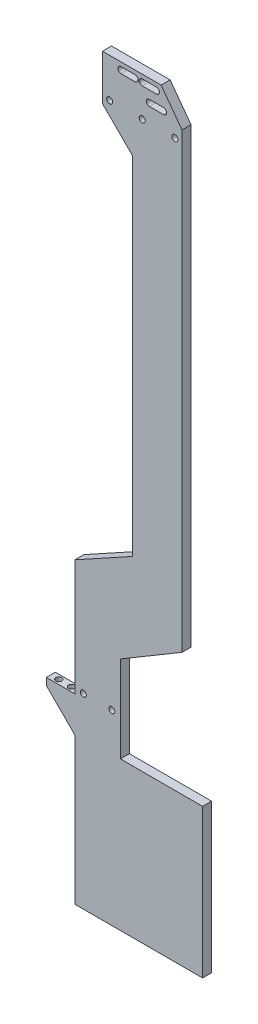
SolidWorks part; units mm, degrees
material "1060 Alloy"
ref_plane "Front Plane" through (0, 0, 0) normal (0, 0, 1) x (1, 0, 0)
ref_plane "Top Plane" through (0, 0, 0) normal (0, 1, 0) x (1, 0, 0)
ref_plane "Right Plane" through (0, 0, 0) normal (1, 0, 0) x (0, 0, -1)
sketch "Sketch1" plane through (0, 0, 0) normal (0, 0, 1) x (1, 0, 0)
  line L0 (-14.5, 164.7863) -> (-29.2, 184.7863) construction
  line L1 (-70.5, 184.7863) -> (-29.2, 184.7863) construction
  line L2 (-70.5, 184.7863) -> (-70.5, 152.7863) construction
  line L3 (-14.5, 164.7863) -> (-14.5, -153.7918) construction
  line L4 (-70.5, 152.7863) -> (-49.5, 131.7863) construction
  line L5 (-49.5, 131.7863) -> (-49.5, -112.8034) construction
  line L6 (-90, -135.1126) -> (-49.5, -112.8034) construction
  line L7 (-14.5, -153.7918) -> (-57.9145, -179.5263) construction
  line L9 (0, -345.1126) -> (-90, -345.1126) construction
  line L11 (-14.5, 164.7863) -> (-29.2, 184.7863)
  line L12 (-70.5, 184.7863) -> (-29.2, 184.7863)
  line L13 (-70.5, 184.7863) -> (-70.5, 152.7863)
  line L14 (-14.5, 164.7863) -> (-14.5, -153.7918)
  line L15 (-70.5, 152.7863) -> (-49.5, 131.7863)
  line L16 (-49.5, 131.7863) -> (-49.5, -112.8034)
  line L17 (-90, -135.1126) -> (-49.5, -112.8034)
  line L18 (-14.5, -153.7918) -> (-57.9145, -179.5263)
  line L19 (-57.9145, -179.5263) -> (-57.9145, -240.4418)
  line L20 (0, -345.1126) -> (-90, -345.1126)
  line L21 (-90, -345.1126) -> (-90, -241.825)
  line L22 (-42.5, 179.7863) -> (-32.5, 179.7863) construction
  line L23 (-42.5, 181.9363) -> (-32.5, 181.9363)
  line L24 (-42.5, 177.6363) -> (-32.5, 177.6363)
  line L25 (-57.5, 179.7863) -> (-47.5, 179.7863) construction
  line L26 (-32.5, 179.7863) -> (-32.5, 175.88) construction
  line L27 (-57.5, 181.9363) -> (-47.5, 181.9363)
  line L28 (-57.5, 177.6363) -> (-47.5, 177.6363)
  line L29 (-37.5, 169.7863) -> (-27.5, 169.7863) construction
  line L30 (-37.5, 171.9363) -> (-27.5, 171.9363)
  line L31 (-37.5, 167.6363) -> (-27.5, 167.6363)
  line L32 (-32.5, 169.7863) -> (-52.5, 169.7863) construction
  line L33 (-32.5, 175.88) -> (-37.5, 175.88) construction
  line L34 (-37.5, 179.7863) -> (-37.5, 175.88) construction
  line L35 (-47.5, 179.7863) -> (-47.5, 175.4879) construction
  line L36 (-47.5, 175.4879) -> (-52.5, 175.4879) construction
  line L37 (-32.5, 174.0404) -> (-32.5, 169.7863) construction
  line L38 (-27.5, 169.7863) -> (-27.5, 174.0404) construction
  line L39 (-27.5, 174.0404) -> (-32.5, 174.0404) construction
  line L40 (-52.5, 175.4879) -> (-52.5, 179.7863) construction
  line L41 (-57.9145, -240.4418) -> (0, -240.4418)
  line L42 (0, -240.4418) -> (0, -345.1126)
  line L43 (-57.9145, -240.4418) -> (0, -240.4418) construction
  line L44 (-90, -216.825) -> (-110, -216.825) construction
  line L45 (-110, -216.825) -> (-110, -221.825) construction
  line L46 (-110, -221.825) -> (-90, -241.825) construction
  line L47 (-90, -216.825) -> (-110, -216.825)
  line L48 (-110, -216.825) -> (-110, -221.825)
  line L49 (-110, -221.825) -> (-90, -241.825)
  line L50 (-90, -216.825) -> (-90, -135.1126)
  line L51 (-90, -216.825) -> (-57.9145, -216.825) construction
  line L52 (-90, -213.65) -> (-57.9145, -213.65) construction
  circle A0 centre (-19.5, 157.2863) radius 2.15 construction
  circle A1 centre (-42.5, 157.2863) radius 2.15 construction
  circle A2 centre (-65.5, 157.2863) radius 2.15 construction
  circle A3 centre (-37.5, 179.7863) radius 2.15 construction
  circle A4 centre (-52.5, 179.7863) radius 2.15 construction
  circle A5 centre (-32.5, 169.7863) radius 2.15 construction
  circle A6 centre (-19.5, 157.2863) radius 2.15
  circle A7 centre (-42.5, 157.2863) radius 2.15
  circle A8 centre (-65.5, 157.2863) radius 2.15
  circle A9 centre (-37.5, 179.7863) radius 2.15 construction
  circle A10 centre (-52.5, 179.7863) radius 2.15 construction
  circle A11 centre (-32.5, 169.7863) radius 2.15 construction
  arc A12 (-42.5, 181.9363) -> (-42.5, 177.6363) centre (-42.5, 179.7863) ccw
  arc A13 (-32.5, 177.6363) -> (-32.5, 181.9363) centre (-32.5, 179.7863) ccw
  arc A14 (-57.5, 181.9363) -> (-57.5, 177.6363) centre (-57.5, 179.7863) ccw
  arc A15 (-47.5, 177.6363) -> (-47.5, 181.9363) centre (-47.5, 179.7863) ccw
  arc A16 (-37.5, 171.9363) -> (-37.5, 167.6363) centre (-37.5, 169.7863) ccw
  arc A17 (-27.5, 167.6363) -> (-27.5, 171.9363) centre (-27.5, 169.7863) ccw
  circle A18 centre (-84, -213.65) radius 2.1
  circle A19 centre (-63.9145, -213.65) radius 2.1
  point P31 (-37.5, 179.7863)
  point P36 (-52.5, 179.7863)
  point P45 (-32.5, 169.7863)
  dimension "D4" = 4.2
  dimension "D1" = 5
  dimension "D2" = 5
  dimension "D3" = 3.175
  dimension "D5" = 6
  dimension "D6" = 6
extrude "Boss-Extrude1" add sketch "Sketch1" along normal blind 6.35
sketch "Sketch2" plane through (0, -216.825, 0) normal (0, 1, 0) x (-1, 0, 0)
  line L0 (90, 3.175) -> (95.5, 3.175) construction
  line L1 (90, 6.35) -> (90, 0) construction
  line L2 (95.5, 3.175) -> (104.5, 3.175) construction
  line L3 (104.5, 3.175) -> (110, 3.175) construction
  line L4 (110, 6.35) -> (110, 0) construction
  circle A0 centre (95.5, 3.175) radius 2.1
  circle A1 centre (104.5, 3.175) radius 2.1
  dimension "D1" = 4.2
  dimension "D2" = 9
extrude "Cut-Extrude1" cut sketch "Sketch2" against normal blind 5
